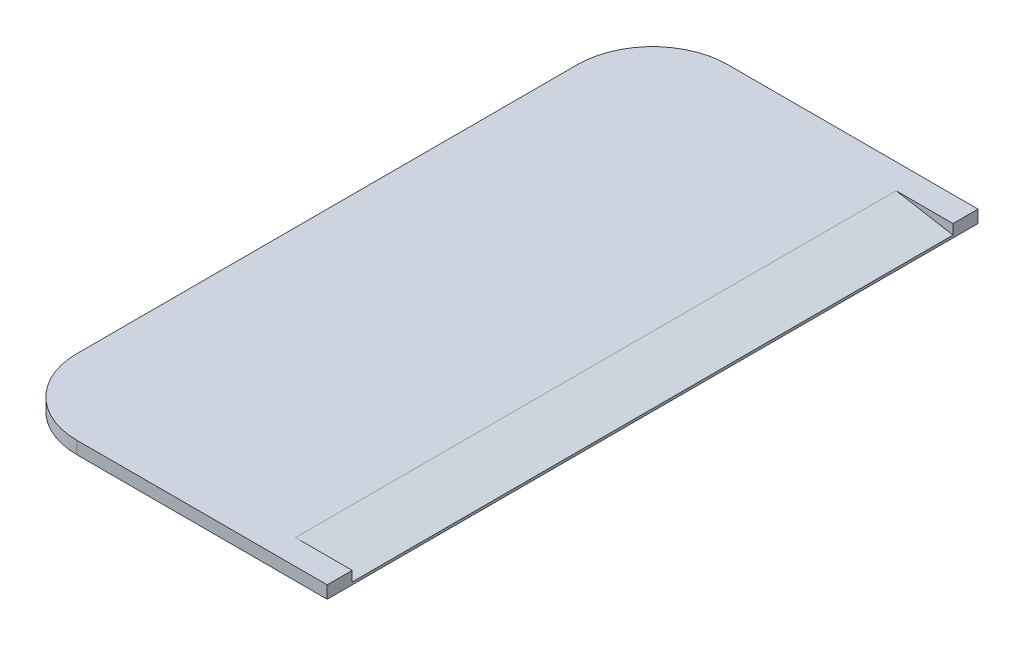
SolidWorks part; units mm, degrees
ref_plane "Front Plane" through (0, 0, 0) normal (0, 0, 1) x (1, 0, 0)
ref_plane "Top Plane" through (0, 0, 0) normal (0, 1, 0) x (1, 0, 0)
ref_plane "Right Plane" through (0, 0, 0) normal (1, 0, 0) x (0, 0, -1)
sketch "Sketch1" plane through (0, 0, 0) normal (0, 1, 0) x (1, 0, 0)
  line L1 (-7, -26) -> (13, -26)
  line L2 (-13, -20) -> (-13, 20)
  line L3 (-7, 26) -> (13, 26)
  line L4 (13, -26) -> (13, 26)
  line L5 (-13, -26) -> (13, 26) construction
  line L6 (-13, 26) -> (13, -26) construction
  arc A0 (-7, -26) -> (-13, -20) centre (-7, -20) cw
  arc A1 (-13, 20) -> (-7, 26) centre (-7, 20) cw
  point P0 (0, 0)
  dimension "D3" = 6
  dimension "D1" = 26
  dimension "D2" = 52
extrude "Boss-Extrude1" add sketch "Sketch1" along normal mid plane 1
sketch "Sketch2" plane through (0, 0, 0) normal (0, 0, 1) x (1, 0, 0)
  line L0 (13, -0.3) -> (8.463, 0.5)
  line L1 (13, 0.5) -> (13, -0.5) construction
  line L2 (-7, 0.5) -> (13, 0.5) construction
  line L7 (8.463, 0.5) -> (13, 0.5)
  line L8 (13, 0.5) -> (13, -0.3)
  dimension "D1" = 0.8
  dimension "D2" = 10
extrude "Cut-Extrude4" cut sketch "Sketch2" against normal mid plane 48
